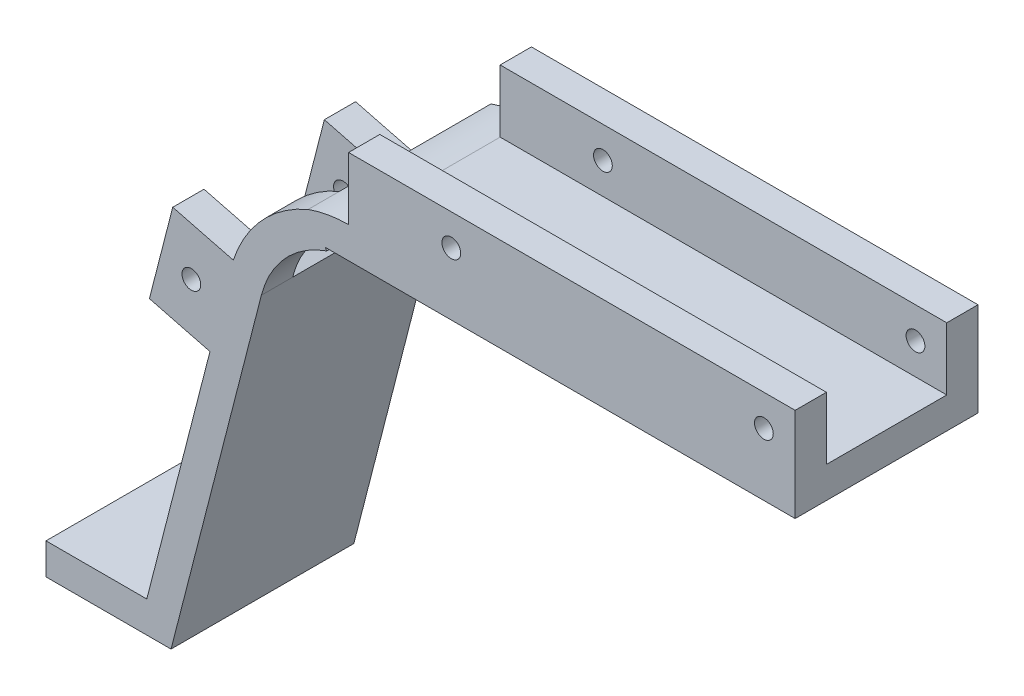
SolidWorks part; units mm, degrees
material "PE High Density"
ref_plane "Front Plane" through (0, 0, 0) normal (0, 0, 1) x (1, 0, 0)
ref_plane "Top Plane" through (0, 0, 0) normal (0, 1, 0) x (1, 0, 0)
ref_plane "Right Plane" through (0, 0, 0) normal (1, 0, 0) x (0, 0, -1)
sketch "Sketch1" plane through (0, 0, 0) normal (0, 0, 1) x (1, 0, 0)
  line L1 (0, 0) -> (120, 0)
  line L2 (0, 0) -> (0, 100)
  line L3 (0, 100) -> (120, 100)
  line L4 (120, 0) -> (120, 100)
  dimension "D1" = 120
  dimension "D2" = 100
extrude "Boss-Extrude1" add sketch "Sketch1" along normal blind 5
sketch "Sketch2" plane through (0, 0, 5) normal (0, 0, 1) x (1, 0, 0)
  line L0 (0, 0) -> (120, 0) construction
  line L3 (83.1194, 4.5558) -> (120, 30.3799) construction
  line L4 (120, 0) -> (120, 100) construction
  arc A0 (75.8063, 15) -> (89.605, 30) centre (48.5614, 53.9097) ccw construction
  arc A1 (83.1194, 4.5558) -> (100.6219, 23.5821) centre (48.5614, 53.9097) ccw
  arc A2 (68.4932, 25.4442) -> (78.588, 36.4179) centre (48.5614, 53.9097) ccw
  arc A3 (68.4932, 25.4442) -> (83.1194, 4.5558) centre (75.8063, 15) ccw
  arc A4 (100.6219, 23.5821) -> (78.588, 36.4179) centre (89.605, 30) ccw
  arc A5 (48.5614, 6.4097) -> (89.605, 30) centre (48.5614, 53.9097) ccw construction
  arc A6 (48.5614, -28.5903) -> (119.8476, 12.3823) centre (48.5614, 53.9097) ccw construction
  arc A7 (48.5614, 41.4097) -> (59.3623, 47.6177) centre (48.5614, 53.9097) ccw construction
  arc A8 (48.5614, 41.4097) -> (48.5614, -28.5903) centre (48.5614, 6.4097) ccw construction
  arc A9 (119.8476, 12.3823) -> (59.3623, 47.6177) centre (89.605, 30) ccw construction
  circle A10 centre (48.5614, 53.9097) radius 2.5
  point P3 (83.5196, 21.7512)
  point P17 (72.2314, 12.7274)
  point P27 (115, 5)
  dimension "D1" = 47.5
  dimension "D3" = 12.75
  dimension "D6" = 5
  dimension "D5" = 35
  dimension "D9" = 5
  dimension "D2" = 15
  dimension "D4" = 30
  dimension "D7" = 5
  dimension "D8" = 35
extrude "Cut-Extrude1" cut sketch "Sketch2" against normal through all
sketch "Sketch3" plane through (0, 0, 0) normal (0, 0, -1) x (-1, 0, 0)
  line L0 (0, 100) -> (0, 0) construction
  line L1 (-120, 0) -> (0, 0)
  line L2 (-120, 0) -> (-120, 1.6)
  line L3 (-120, 1.6) -> (0, 1.6)
  line L4 (0, 0) -> (0, 1.6)
  dimension "D1" = 1.6
extrude "Boss-Extrude2" [suppressed] add sketch "Sketch3" along normal blind 30
sketch "Sketch4" plane through (0, 0, 5) normal (0, 0, 1) x (1, 0, 0)
  line L0 (89.605, 30) -> (48.5614, 53.9097) construction
  line L1 (48.5614, 53.9097) -> (75.8063, 15) construction
  line L2 (92.6251, 35.1845) -> (51.5816, 59.0942) construction
  line L3 (52.6571, 56.7776) -> (79.902, 17.8679) construction
  line L4 (120, 0) -> (120, 100) construction
  line L5 (0, 0) -> (120, 0) construction
  arc A0 (65.8054, 38) -> (73, 46.617) centre (63.0497, 47.6128) ccw construction
  arc A1 (66.4943, 35.5968) -> (75.4876, 46.368) centre (63.0497, 47.6128) ccw
  arc A2 (65.1165, 40.4032) -> (70.5124, 46.8659) centre (63.0497, 47.6128) ccw
  arc A3 (65.1165, 40.4032) -> (66.4943, 35.5968) centre (65.8054, 38) ccw
  arc A4 (75.4876, 46.368) -> (70.5124, 46.8659) centre (73, 46.617) ccw
  point P13 (70.7259, 41.2037)
  dimension "D3" = 2.5
  dimension "D4" = 10
  dimension "D5" = 47
  dimension "D6" = 38
  dimension "D1" = 6
  dimension "D2" = 5
extrude "Cut-Extrude2" [suppressed] cut sketch "Sketch4" against normal through all
sketch "Sketch5" plane through (0, 0, 5) normal (0, 0, 1) x (1, 0, 0)
  line L0 (120, 73) -> (48.5614, 73)
  line L1 (120, 0) -> (120, 100) construction
  line L2 (30.0716, 58.6603) -> (15, 0)
  line L3 (0, 0) -> (120, 0) construction
  line L4 (15, 0) -> (0, 0)
  line L5 (0, 0) -> (0, 100)
  line L6 (0, 100) -> (120, 100)
  line L7 (120, 100) -> (120, 73)
  arc A0 (48.5614, 73) -> (30.0716, 58.6603) centre (48.5614, 53.9097) ccw
  circle A1 centre (48.5614, 53.9097) radius 2.5 construction
  dimension "D1" = 15
  dimension "D2" = 73
extrude "Cut-Extrude3" cut sketch "Sketch5" against normal blind 10
sketch "Sketch7" plane through (0, 0, 0) normal (0, 0, -1) x (-1, 0, 0)
  line L0 (-15, 0) -> (-30.1239, 58.8638)
  line L1 (-120, 73) -> (-48.5614, 73)
  line L2 (-120, 73) -> (-120, 68)
  line L3 (-120, 68) -> (-44.7991, 68)
  line L5 (-30.0716, 58.6603) -> (-15, 0) construction
  line L7 (-34.6143, 56.248) -> (-20.1624, 0)
  line L8 (-15, 0) -> (-120, 0) construction
  line L9 (-20.1624, 0) -> (-15, 0)
  line L10 (-89.605, 30) -> (-48.5614, 53.9097) construction
  line L11 (-48.5614, 53.9097) -> (-29.5237, 65) construction
  line L12 (-75.8063, 15) -> (-48.5614, 53.9097) construction
  line L13 (-48.5614, 53.9097) -> (-34.8806, 73.4479) construction
  line L14 (-79.902, 17.8679) -> (-52.6571, 56.7776) construction
  line L15 (-52.6571, 56.7776) -> (-38.9763, 76.3158) construction
  line L16 (-87.0882, 25.6796) -> (-46.0446, 49.5893) construction
  line L17 (-46.0446, 49.5893) -> (-27.0069, 60.6796) construction
  line L18 (-44.7991, 68) -> (-42.0897, 71.8695)
  line L19 (-34.6143, 56.248) -> (-30.1239, 58.8638)
  arc A0 (-48.5614, 73) -> (-42.0897, 71.8695) centre (-48.5614, 53.9097) cw
  arc A1 (-30.0716, 58.6603) -> (-48.5614, 73) centre (-48.5614, 53.9097) ccw construction
  dimension "D2" = 5
  dimension "D4" = 5
  dimension "D5" = 5
  dimension "D6" = 5
extrude "Boss-Extrude3" add sketch "Sketch7" along normal blind 29.25
sketch "Sketch8" plane through (0, 0, -29.25) normal (0, 0, -1) x (-1, 0, 0)
  line L0 (-20.1624, 0) -> (-15, 0) construction
  line L1 (-20.1624, 0) -> (-0.1624, 0)
  line L2 (-20.1624, 0) -> (-20.1624, 5)
  line L3 (-20.1624, 5) -> (-0.1624, 5)
  line L4 (-0.1624, 0) -> (-0.1624, 5)
  line L5 (-34.6143, 56.248) -> (-20.1624, 0) construction
  dimension "D1" = 20
  dimension "D2" = 5
extrude "Boss-Extrude4" add sketch "Sketch8" against normal through all
sketch "Sketch9" plane through (0, 73, 0) normal (0, 1, 0) x (1, 0, 0)
  line L0 (48.5614, 29.25) -> (120, 29.25) construction
  line L7 (120, 29.25) -> (120, -5) construction
  circle A0 centre (108, 21.25) radius 2.5
  dimension "D3" = 5
  dimension "D1" = 8
  dimension "D2" = 12
sketch "Sketch10" plane through (0, 0, 0) normal (0, 0, -1) x (-1, 0, 0)
  line L5 (-45.0697, 67.6137) -> (-42.0897, 71.8695)
  line L7 (-44.7991, 68) -> (-42.0897, 71.8695) construction
  line L8 (-44.7991, 68) -> (-42.0897, 71.8695) construction
  line L9 (-30.125, 58.8632) -> (-34.6143, 56.248)
  arc A2 (-42.0897, 71.8695) -> (-30.125, 58.8632) centre (-50.4013, 52.2172) cw
  circle A3 centre (-48.5614, 53.9097) radius 2.5 construction
  arc A6 (-45.0697, 67.6137) -> (-34.6143, 56.248) centre (-50.4013, 52.2172) cw
extrude "Boss-Extrude5" add sketch "Sketch10" along normal blind 5
sketch "Sketch11" plane through (120, 0, 0) normal (1, 0, 0) x (0, 0, -1)
  line L0 (-5, 0) -> (0, 0) construction
  line L1 (-5, 0) -> (0, 0)
  line L2 (-5, 0) -> (-5, 73)
  line L3 (-5, 73) -> (0, 73)
  line L4 (0, 0) -> (0, 73)
  line L5 (-5, 0) -> (-5, 73) construction
  line L6 (29.25, 73) -> (-5, 73) construction
extrude "Cut-Extrude6" cut sketch "Sketch11" against normal through all both and the other way through all
sketch "Sketch12" plane through (0, 5, 0) normal (0, 1, 0) x (1, 0, 0)
  line L0 (0.1624, 0) -> (0.1624, 29.25) construction
  line L3 (0.1624, 0) -> (0.1624, 29.25) construction
  circle A0 centre (7.6624, 14.625) radius 1.5
  point P7 (0.1624, 14.625)
  dimension "D1" = 3
  dimension "D3" = 7.5
extrude "Cut-Extrude7" cut sketch "Sketch12" against normal through all both
sketch "Sketch13" plane through (0, 73, 0) normal (0, 1, 0) x (1, 0, 0)
  line L0 (120, 29.25) -> (120, 0) construction
  line L1 (48.5614, 0) -> (120, 0)
  line L2 (48.5614, 0) -> (48.5614, 5)
  line L3 (48.5614, 5) -> (120, 5)
  line L4 (120, 0) -> (120, 5)
  line L6 (48.5614, 29.25) -> (120, 29.25)
  line L7 (48.5614, 29.25) -> (48.5614, 24.25)
  line L8 (48.5614, 24.25) -> (120, 24.25)
  line L9 (120, 29.25) -> (120, 24.25)
  dimension "D1" = 5
  dimension "D2" = 5
extrude "Boss-Extrude6" add sketch "Sketch13" along normal blind 10
sketch "Sketch14" plane through (0, 0, 0) normal (0, 0, 1) x (1, 0, 0)
  line L1 (48.5614, 83) -> (120, 83) construction
  line L2 (120, 83) -> (120, 68) construction
  circle A0 centre (65, 78) radius 1.5
  circle A1 centre (115, 78) radius 1.5
  dimension "D1" = 3
  dimension "D2" = 3
  dimension "D4" = 5
  dimension "D3" = 50
  dimension "D5" = 5
extrude "Cut-Extrude8" cut sketch "Sketch14" against normal through all
sketch "Sketch15" plane through (14.0711, -3.6153, 0) normal (-0.9685, 0.2488, 0) x (0, 0, 1)
  line L0 (0, 8.8951) -> (0, 64.5084) construction
  line L1 (-5, 64.5081) -> (0, 64.5081)
  line L2 (-5, 64.5081) -> (-5, 49.5084)
  line L3 (-5, 49.5084) -> (0, 49.5084)
  line L4 (0, 64.5081) -> (0, 49.5084)
  line L5 (-29.25, 64.5084) -> (-24.25, 64.5084)
  line L6 (-29.25, 64.5084) -> (-29.25, 49.5084)
  line L7 (-29.25, 49.5084) -> (-24.25, 49.5084)
  line L8 (-24.25, 64.5084) -> (-24.25, 49.5084)
  dimension "D1" = 15
extrude "Boss-Extrude7" add sketch "Sketch15" along normal blind 10
sketch "Sketch17" plane through (0, 0, 0) normal (0, 0, 1) x (1, 0, 0)
  line L0 (16.7058, 46.8242) -> (20.4384, 61.352) construction
  line L1 (16.7058, 46.8242) -> (26.3912, 44.3357) construction
  circle A0 centre (23.4149, 52.844) radius 1.5
  dimension "D3" = 3
  dimension "D1" = 5
  dimension "D2" = 7.5
extrude "Cut-Extrude9" cut sketch "Sketch17" against normal through all
